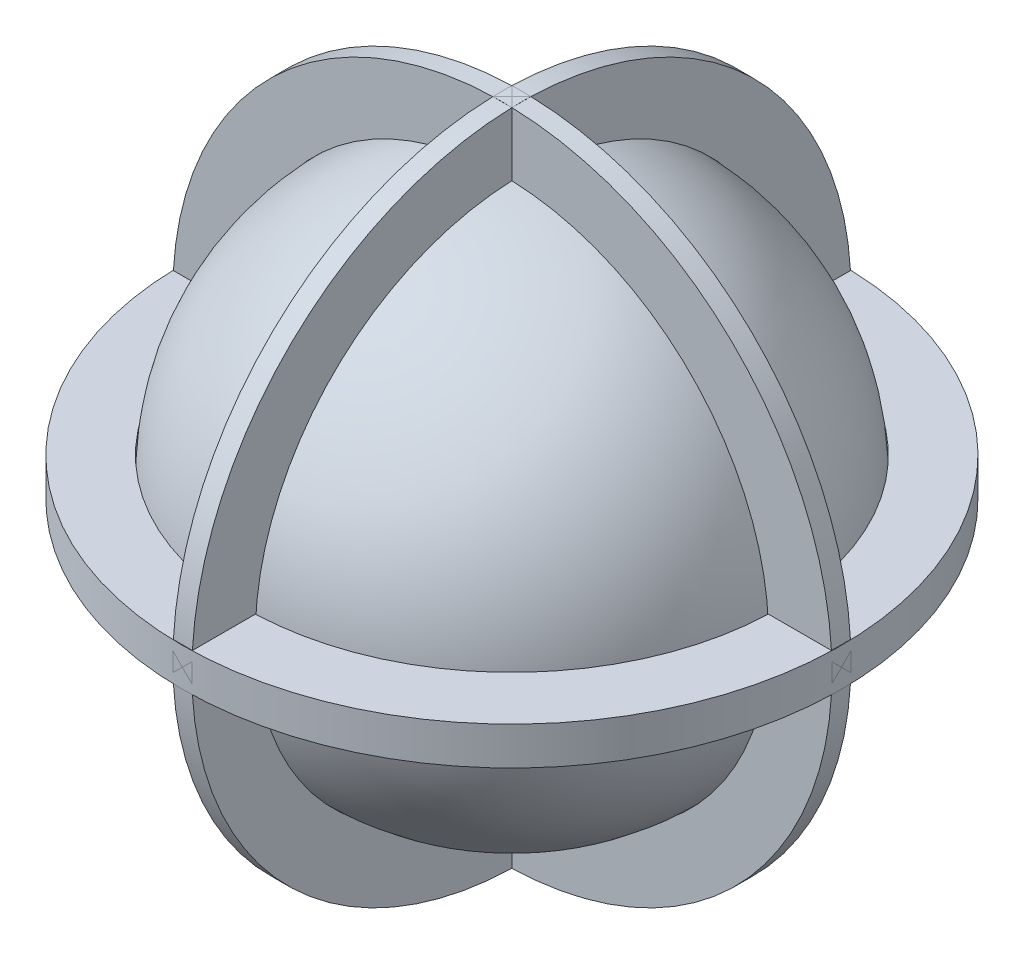
SolidWorks part; units mm, degrees
ref_plane "Front Plane" through (0, 0, 0) normal (0, 0, 1) x (1, 0, 0)
ref_plane "Top Plane" through (0, 0, 0) normal (0, 1, 0) x (1, 0, 0)
ref_plane "Right Plane" through (0, 0, 0) normal (1, 0, 0) x (0, 0, -1)
sketch "Sketch1" plane through (0, 0, 0) normal (0, 0, 1) x (1, 0, 0)
  line L0 (0, 0) -> (0, 50000)
  circle A0 centre (0, 0) radius 40
  circle A1 centre (0, 0) radius 42
  dimension "D1" = 80
  dimension "D2" = 2
revolve "Revolve3" add sketch "Sketch1" angle 360 about L0
sketch "Sketch2" plane through (0, 0, 0) normal (0, 0, 1) x (1, 0, 0)
  circle A0 centre (0, 0) radius 42 construction
  circle A1 centre (0, 0) radius 42
  circle A2 centre (0, 0) radius 52
  dimension "D1" = 10
extrude "Boss-Extrude1" add sketch "Sketch2" along normal mid plane 3 separate body
sketch "Sketch4" plane through (0, 0, 0) normal (1, 0, 0) x (0, 0, -1)
  circle A0 centre (0, 0) radius 42 construction
  circle A1 centre (0, 0) radius 42
  circle A2 centre (0, 0) radius 52
  dimension "D1" = 10
extrude "Boss-Extrude2" add sketch "Sketch4" along normal mid plane 3
sketch "Sketch5" plane through (0, 0, 0) normal (0, 1, 0) x (1, 0, 0)
  circle A0 centre (0, 0) radius 42 construction
  circle A1 centre (0, 0) radius 42
  circle A2 centre (0, 0) radius 52
  dimension "D1" = 10
extrude "Boss-Extrude3" add sketch "Sketch5" along normal mid plane 6
